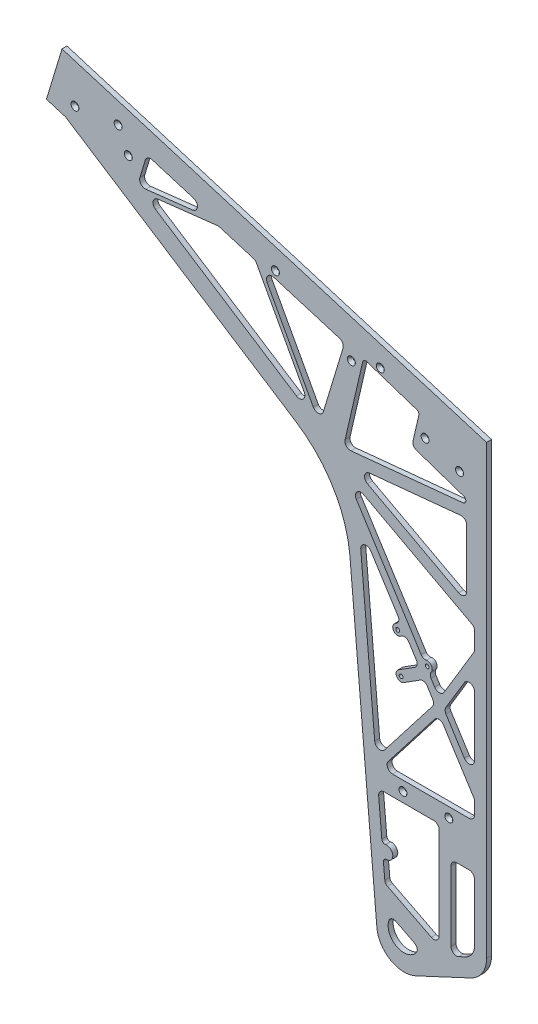
SolidWorks part; units mm, degrees
material "Beech"
ref_plane "Front Plane" through (0, 0, 0) normal (0, 0, 1) x (1, 0, 0)
ref_plane "Top Plane" through (0, 0, 0) normal (0, 1, 0) x (1, 0, 0)
ref_plane "Right Plane" through (0, 0, 0) normal (1, 0, 0) x (0, 0, -1)
sketch "Sketch2" plane through (0, 0, 0) normal (0, 0, 1) x (1, 0, 0)
  line L3 (52.061, -347.2658) -> (17.0528, -329.4943)
  line L18 (0.7275, -204.3995) -> (4.7586, -250.4747)
  line L19 (71, -196.7894) -> (7.7009, -196.7894)
  line L20 (78, -320.9929) -> (78, -203.7894)
  line L21 (8.8549, -297.2958) -> (67.8314, -327.2347)
  line L22 (6.8503, -274.3834) -> (8.8549, -297.2958)
  line L23 (11.4827, -269.9628) -> (10.4865, -270.05)
  line L24 (9.092, -254.1109) -> (10.0882, -254.0237)
  line L27 (123, -309.0696) -> (123, -235.7894)
  line L28 (102.9583, -331.1566) -> (111.4524, -327.1958)
  line L29 (93, -235.7894) -> (93, -324.8124)
  line L30 (116, -228.7894) -> (100, -228.7894)
  line L35 (123, -164.7894) -> (123, -147.491)
  line L36 (18.4936, -171.7894) -> (116, -171.7894)
  line L37 (71.9182, -84.5103) -> (12.9629, -160.4984)
  line L38 (123, -147.491) -> (83.3585, -85.0495)
  line L41 (123, -104.7468) -> (123, -28.6549)
  line L42 (86.5792, -71.4649) -> (110.0903, -108.4986)
  line L43 (110.0027, -25.0448) -> (86.4916, -64.103)
  line L47 (-22.0887, 56.3913) -> (-4.3233, -146.6681)
  line L48 (69.6883, -63.5168) -> (-9.2057, 60.7532)
  line L49 (8.1807, -150.3489) -> (69.3092, -71.5595)
  line L55 (84.1071, -48.674) -> (123, 15.9373)
  line L56 (-27.7256, 108.5825) -> (72.2002, -48.8158)
  line L57 (123, 42.7347) -> (-18.5117, 118.5054)
  line L58 (123, 15.9373) -> (123, 42.7347)
  line L61 (105.3136, 157.4535) -> (-10.9295, 145.9995)
  line L62 (113, 76.7923) -> (113, 150.4873)
  line L63 (-13.5473, 132.8622) -> (102.6958, 70.6213)
  line L71 (49.3928, 246.173) -> (-14.4833, 267.3378)
  line L72 (43.1791, 203.129) -> (52.0322, 241.4762)
  line L73 (109.2468, 180.5917) -> (43.1791, 203.129)
  line L74 (-34.5621, 158.7435) -> (108.3476, 172.8251)
  line L75 (-19.6388, 264.4406) -> (-42.0691, 167.2844)
  line L99 (-35.9297, 42.1538) -> (-1.5139, -351.2208)
  line L100 (48.0382, -379.8296) -> (118.2139, -347.1062)
  line L101 (138.3789, -315.4534) -> (138.3789, 254.5381)
  line L102 (138.3789, 254.5381) -> (-403.0991, 418.4193)
  line L103 (-403.0991, 418.4193) -> (-422.935, 352.8794)
  line L104 (-422.935, 352.8794) -> (-398.6241, 345.5216)
  line L105 (-398.6241, 345.5216) -> (-105.0266, 156.03)
  line L106 (-35.9297, 42.1538) -> (-1.5139, -351.2208)
  line L107 (48.0382, -379.8296) -> (118.2139, -347.1062)
  line L108 (138.3789, -315.4534) -> (138.3789, 254.5381)
  line L109 (138.3789, 254.5381) -> (-403.0991, 418.4193)
  line L110 (-403.0991, 418.4193) -> (-422.935, 352.8794)
  line L111 (-422.935, 352.8794) -> (-398.6241, 345.5216)
  line L112 (-398.6241, 345.5216) -> (-105.0266, 156.03)
  arc A2 (17.0528, -329.4943) -> (52.061, -347.2658) centre (32.8243, -341.7931) ccw
  arc A14 (4.7586, -250.4747) -> (9.092, -254.1109) centre (8.7434, -250.1261) ccw
  arc A15 (7.7009, -196.7894) -> (0.7275, -204.3995) centre (7.7009, -203.7894) ccw
  arc A16 (78, -203.7894) -> (71, -196.7894) centre (71, -203.7894) ccw
  arc A17 (67.8314, -327.2347) -> (78, -320.9929) centre (71, -320.9929) ccw
  arc A18 (10.4865, -270.05) -> (6.8503, -274.3834) centre (10.8351, -274.0347) ccw
  arc A19 (11.4827, -269.9628) -> (10.0882, -254.0237) centre (10.7854, -261.9933) ccw
  arc A22 (123, -235.7894) -> (116, -228.7894) centre (116, -235.7894) ccw
  arc A23 (111.4524, -327.1958) -> (123, -309.0696) centre (103, -309.0696) ccw
  arc A24 (93, -324.8124) -> (102.9583, -331.1566) centre (100, -324.8124) ccw
  arc A25 (100, -228.7894) -> (93, -235.7894) centre (100, -235.7894) ccw
  arc A28 (116, -171.7894) -> (123, -164.7894) centre (116, -164.7894) ccw
  arc A29 (12.9629, -160.4984) -> (18.4936, -171.7894) centre (18.4936, -164.7894) ccw
  arc A30 (83.3585, -85.0495) -> (71.9182, -84.5103) centre (77.4488, -88.8013) ccw
  arc A34 (110.0903, -108.4986) -> (123, -104.7468) centre (116, -104.7468) ccw
  arc A35 (86.4916, -64.103) -> (86.5792, -71.4649) centre (92.4888, -67.7131) ccw
  arc A36 (123, -28.6549) -> (110.0027, -25.0448) centre (116, -28.6549) ccw
  arc A40 (-4.3233, -146.6681) -> (8.1807, -150.3489) centre (2.65, -146.058) ccw
  arc A41 (-9.2057, 60.7532) -> (-22.0887, 56.3913) centre (-15.1153, 57.0014) ccw
  arc A42 (69.3092, -71.5595) -> (69.6883, -63.5168) centre (63.7786, -67.2686) ccw
  arc A44 (72.2002, -48.8158) -> (84.1071, -48.674) centre (78.1098, -45.064) ccw
  arc A45 (-18.5117, 118.5054) -> (-27.7256, 108.5825) centre (-21.8159, 112.3343) ccw
  arc A50 (113, 150.4873) -> (105.3136, 157.4535) centre (106, 150.4873) ccw
  arc A51 (102.6958, 70.6213) -> (113, 76.7923) centre (106, 76.7923) ccw
  arc A52 (-10.9295, 145.9995) -> (-13.5473, 132.8622) centre (-10.2431, 139.0332) ccw
  arc A58 (-14.4833, 267.3378) -> (-19.6388, 264.4406) centre (-15.7414, 263.5408) ccw
  arc A59 (52.0322, 241.4762) -> (49.3928, 246.173) centre (48.1347, 242.376) ccw
  arc A60 (108.3476, 172.8251) -> (109.2468, 180.5917) centre (107.9554, 176.8059) ccw
  arc A61 (-42.0691, 167.2844) -> (-34.5621, 158.7435) centre (-35.2485, 165.7098) ccw
  arc A77 (-35.9297, 42.1538) -> (-105.0266, 156.03) centre (-187.6695, 27.9835) ccw
  arc A78 (-1.5139, -351.2208) -> (48.0382, -379.8296) centre (33.2782, -348.1768) ccw
  arc A79 (118.2139, -347.1062) -> (138.3789, -315.4534) centre (103.4539, -315.4534) ccw
  arc A80 (-35.9297, 42.1538) -> (-105.0266, 156.03) centre (-187.6695, 27.9835) ccw
  arc A81 (-1.5139, -351.2208) -> (48.0382, -379.8296) centre (33.2782, -348.1768) ccw
  arc A82 (118.2139, -347.1062) -> (138.3789, -315.4534) centre (103.4539, -315.4534) ccw
  line B0 (-69.7843, 184.37) -> (-44.7069, 267.0652)
  line B1 (-141.4417, 291.191) -> (-82.6325, 183.0571)
  line B2 (-49.3742, 275.7954) -> (-133.2609, 301.2341)
  line B3 (-94.2196, 193.8972) -> (-156.4138, 308.2553)
  line B4 (-283.8496, 300.7813) -> (-104.1681, 184.6735)
  line B5 (-203.4472, 322.5182) -> (-280.8504, 313.6148)
  line B6 (-156.4138, 308.2553) -> (-203.4472, 322.5182)
  line B7 (-235.2905, 337.3996) -> (-288.1216, 353.4207)
  line B8 (-296.2966, 316.871) -> (-236.522, 323.7467)
  line B9 (-296.8518, 348.7534) -> (-303.7953, 325.8566)
  arc B10 (-44.7069, 267.0652) -> (-49.3742, 275.7954) centre (-51.4056, 269.0966) ccw
  arc B11 (-82.6325, 183.0571) -> (-69.7843, 184.37) centre (-76.4831, 186.4014) ccw
  arc B12 (-133.2609, 301.2341) -> (-141.4417, 291.191) centre (-135.2923, 294.5354) ccw
  arc B13 (-104.1681, 184.6735) -> (-94.2196, 193.8972) centre (-100.369, 190.5528) ccw
  arc B14 (-280.8504, 313.6148) -> (-283.8496, 300.7813) centre (-280.0505, 306.6606) ccw
  arc B15 (-236.522, 323.7467) -> (-235.2905, 337.3996) centre (-237.3219, 330.7009) ccw
  arc B16 (-303.7953, 325.8566) -> (-296.2966, 316.871) centre (-297.0965, 323.8251) ccw
  arc B17 (-288.1216, 353.4207) -> (-296.8518, 348.7534) centre (-290.153, 346.7219) ccw
  dimension "D13" = 0
sketch_block_instance "Block1-1"
sketch_block "Block1" parameters "D4"=7, "D1"=23.432, "D2"=23.9265, "D3"=55.2069
extrude "Boss-Extrude1" add sketch "Sketch2" along normal blind 6.35
sketch "Sketch3" plane through (0, 0, 6.35) normal (0, 0, 1) x (1, 0, 0)
  line L25 (32.2931, -4.6137) -> (25.0263, -9.2271) construction
  line L26 (69.6883, -63.5168) -> (-9.2057, 60.7532) construction
  line L27 (35.6965, -9.9746) -> (28.4297, -14.588)
  line L28 (28.8896, 0.7472) -> (21.6228, -3.8662)
  line L29 (29.3174, -58.2747) -> (55.7191, -41.5133) construction
  line L30 (25.914, -52.9138) -> (52.3157, -36.1524)
  line L31 (32.7208, -63.6356) -> (59.1225, -46.8742)
  line L32 (62.6488, -30.6471) -> (61.2353, -31.5444) construction
  line L33 (-27.7256, 108.5825) -> (72.2002, -48.8158) construction
  line L34 (66.0522, -36.008) -> (64.6387, -36.9053)
  line L35 (59.2454, -25.2862) -> (57.8319, -26.1835)
  arc A13 (35.6965, -9.9746) -> (28.8896, 0.7472) centre (32.2931, -4.6137) ccw
  arc A14 (21.6228, -3.8662) -> (28.4297, -14.588) centre (25.0263, -9.2271) ccw
  arc A15 (25.914, -52.9138) -> (32.7208, -63.6356) centre (29.3174, -58.2747) ccw
  arc A16 (59.1225, -46.8742) -> (52.3157, -36.1524) centre (55.7191, -41.5133) ccw
  arc A17 (66.0522, -36.008) -> (59.2454, -25.2862) centre (62.6488, -30.6471) ccw
  arc A18 (57.8319, -26.1835) -> (64.6387, -36.9053) centre (61.2353, -31.5444) ccw
  point P6 (28.6597, -6.9204)
  point P13 (42.5182, -49.894)
  point P20 (61.942, -31.0957)
  dimension "D2" = 6.35
extrude "Boss-Extrude3" add sketch "Sketch3" against normal through all contours A18 A16 L30 A15 L31 | L35 A18 A16 L34 A17 | L28 A14 L27 A13
fillet "Fillet2" radius 6.35 15 edges at (-203.4472, 322.5182, 3.175) (-156.4138, 308.2553, 3.175) (43.1791, 203.129, 3.175) (123, 42.7347, 3.175) (123, 15.9373, 3.175) (123, -147.491, 3.175) (8.8549, -297.2958, 3.175) (52.061, -347.2658, 3.175) (17.0528, -329.4943, 3.175) (64.6387, -36.9053, 3.175) (57.8319, -26.1835, 3.175) (28.8896, 0.7472, 3.175) (35.6965, -9.9746, 3.175) (52.3157, -36.1524, 3.175) (59.1225, -46.8742, 3.175)
hole_wizard "#8 Clearance Hole1" positions "Sketch4" profile "Sketch5" hole size "#8" standard "ANSI Inch" end condition up to next
sketch "Sketch4" plane through (0, 0, 6.35) normal (0, 0, 1) x (1, 0, 0)
  circle A0 centre (25.0263, -9.2271) radius 2.4574 construction
  circle A1 centre (29.3174, -58.2747) radius 2.4574 construction
  circle A2 centre (62.6488, -30.6471) radius 2.4574 construction
  point P0 (62.6488, -30.6471)
  point P2 (29.3174, -58.2747)
  point P4 (25.0263, -9.2271)
sketch "Sketch5" plane through (62.6488, -30.6471, 6.35) normal (1, 0, 0) x (0, -1, 0)
  line L0 (0, 0) -> (0, 6.35)
  line L1 (0, 6.35) -> (2.4574, 6.35)
  line L2 (2.4574, 6.35) -> (2.4574, 0)
  line L5 (2.4574, 0) -> (0, 0)
  line L11 (0, -6.35) -> (0, 107.95) construction
  dimension "Thru Hole Dia." = 4.9149
  dimension "Thru Hole Depth" = 6.35
hole_wizard "Hole1" positions "Sketch6" profile "Sketch7" legacy
sketch "Sketch6" plane through (277.2867, -215.2871, 6.35) normal (0, 0, 1) x (-0.09, 0.9959, 0)
  line L0 (54.6742, 260.7254) -> (44.8416, 151.8686) construction
  line L6 (458.2175, 188.8136) -> (426.7882, 117.3689) construction
  line L11 (486.0396, 272.5028) -> (513.4071, 262.4897) construction
  line L19 (643.2075, 626.7743) -> (602.3132, 525.5573) construction
  line L24 (664.0363, 618.3589) -> (454.7061, 100.2486) construction
  line L28 (664.0363, 618.3589) -> (611.7037, 488.8313)
  line L29 (611.7037, 488.8313) -> (559.3712, 359.3037)
  line L30 (559.3712, 359.3037) -> (507.0387, 229.7761)
  line L31 (507.0387, 229.7761) -> (454.7061, 100.2486)
  line L33 (513.4071, 262.4897) -> (486.0396, 272.5028)
  point P12 (52.9605, 241.7526)
  point P14 (47.6978, 183.4898)
  point P29 (434.4591, 134.8062)
  point P31 (453.1036, 177.1887)
  point P48 (499.7233, 267.4963)
  point P79 (636.0712, 609.1114)
  point P81 (609.4494, 543.2202)
  point P98 (559.3712, 359.3037)
  point P100 (507.0387, 229.7761)
  point P112 (637.87, 553.5951)
  point P122 (0, 0)
  point P126 (499.7233, 267.4963)
  point P127 (0, 0)
  point P128 (0, 0)
  point P129 (484.7752, 272.5028)
  dimension "D1" = 19.05
  dimension "D2" = 31.75
  dimension "D3" = 12.7
  dimension "D4" = 19.05
  dimension "D5" = 19.05
  dimension "D6" = 19.05
sketch "Sketch7" plane through (-331.4463, 370.1954, 6.35) normal (1, 0, 0) x (0, -1, 0)
  line L0 (0, 0) -> (0, 32.7039)
  line L1 (0, 32.7039) -> (1.5875, 31.75)
  line L2 (1.5875, 31.75) -> (1.5875, 4.0177)
  line L3 (1.5875, 4.0177) -> (5.08, 0)
  line L4 (5.08, 0) -> (0, 0)
  line L5 (0, -14.3089) -> (0, 102.4216) construction
  line L6 (0, 32.7039) -> (-1.5875, 31.75) construction
  line L7 (-1.5875, 4.0177) -> (-5.08, 0) construction
  dimension "Diameter" = 3.175
  dimension "Depth" = 31.75
  dimension "C-Sink Diameter" = 10.16
  dimension "C-Sink Angle" = 82
  dimension "Drill Angle" = 118
